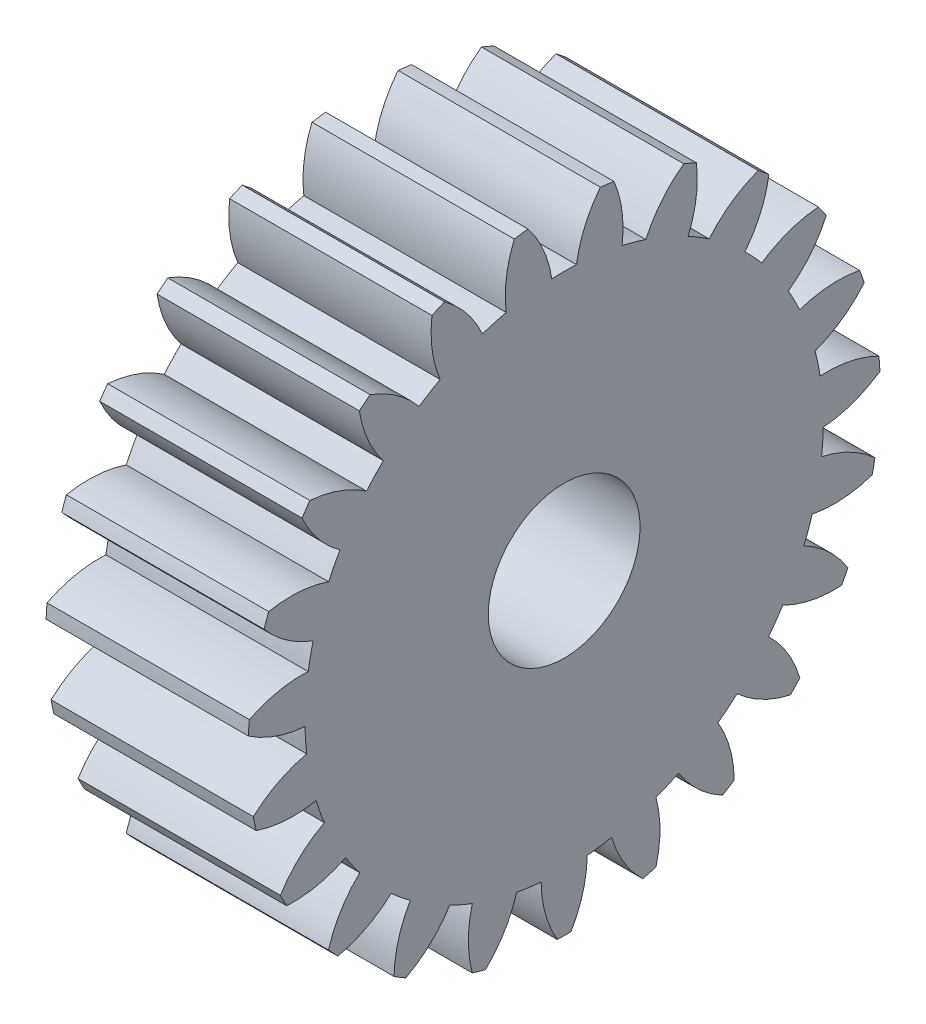
SolidWorks part; units mm, degrees
ref_plane "Plane1" through (0, 0, 0) normal (0, 0, 1) x (1, 0, 0)
ref_plane "Plane2" through (0, 0, 0) normal (0, 1, 0) x (1, 0, 0)
ref_plane "Plane3" through (0, 0, 0) normal (1, 0, 0) x (0, 0, -1)
other "Configuration Table"
sketch "HoldingSke" plane through (0, 0, 0) normal (0, 1, 0) x (1, 0, 0)
  line L0 (0, 0) -> (0.9205, -0.3907)
  line L1 (-15, 0) -> (100, 0) construction
  line L2 (0, 0) -> (-2.1039, 2.3779)
  line L3 (0, 0) -> (-11.863, 4.5341)
  line L4 (0, 0) -> (7.9495, 3.3744)
  line L5 (0, 0) -> (-46.8476, -17.4728)
  line L6 (0, 0) -> (-6.6317, -4.4744)
  line L7 (-2.1039, 2.3779) -> (8.6586, 51.2059)
  line L8 (-76.2, 54.61) -> (-75.2, 54.61)
  line L9 (-71.009, 38.7566) -> (-53.1078, 45.2721)
  line L10 (-76.2, 71.12) -> (104.1128, 71.12)
  line L11 (0, 0) -> (-8, 0)
  line L12 (-76.2, 101.6) -> (-76.162, 101.6)
  line L13 (24.9733, 27.94) -> (52.9518, 28.4284)
  line L14 (24.9733, 27.94) -> (24.9743, 27.94)
  line L15 (24.9733, 27.94) -> (100.4006, 29.5858)
  line L16 (-63.627, -1) -> (-12.827, -1)
  circle A0 centre (0, 0) radius 3
  circle A1 centre (0, 0) radius 10.249
  circle A2 centre (0, 0) radius 37.5
  circle A3 centre (0, 0) radius 3
  dimension "MHD" = 20.498
  dimension "Hub_dia" = 75
  dimension "Bore" = 6
  dimension "MBD" = 6
  dimension "Num_teeth" = 23
  dimension "Pitch" = 1
  dimension "Overall_len" = 50
  dimension "Show_teeth" = 23
  dimension "Thickness" = 8
  dimension "OAL" = 50.0001
  dimension "T_dim" = 1
  dimension "Ap" = 20
  dimension "H" = 19.05
  dimension "Pitch_radius" = 180.3128
  dimension "Width" = 8
  dimension "Backlash" = 0.038
  dimension "Addendum_fac" = 1
  dimension "Dedendum_fac" = 1.25
  dimension "Clearance_fac" = 0.25
  dimension "Dedendum_add" = 0.001
  dimension "Module" = 1
sketch "BasProSke" plane through (0, 0, 0) normal (0, 1, 0) x (1, 0, 0)
  line L0 (-10, 0) -> (60, 0) construction
  line L1 (0, 0) -> (0, 12.5)
  line L2 (0, 0) -> (8, 0)
  line L3 (8, 0) -> (8, 12.5)
  line L4 (8, 12.5) -> (0, 12.5)
  dimension "Thickness" = 8
  dimension "Diameter" = 25
revolve "Base-Revolve" add sketch "BasProSke" angle 360 about L0
sketch "TooCutSke" plane through (0, 0, 0) normal (1, 0, 0) x (0, 0, -1)
  line L1 (0, 0) -> (0, 107) construction
  line L2 (0, 0) -> (-0.8513, 11.4685) construction
  line L3 (0, 0) -> (-3.1257, 22.7413) construction
  line L4 (-0.8513, 11.4685) -> (-1.5629, 11.3706) construction
  arc A0 (0.4871, 10.2374) -> (-0.4871, 10.2374) centre (0, 0) ccw
  arc A1 (1.4505, 12.4411) -> (-1.4505, 12.4411) centre (0, 0) ccw
  circle A2 centre (0, 0) radius 11.5 construction
  circle A3 centre (0, 0) radius 10.8065 construction
  arc A4 (-0.4871, 10.2374) -> (-1.4505, 12.4411) centre (-5.037, 9.5608) ccw
  arc A5 (1.4505, 12.4411) -> (0.4871, 10.2374) centre (5.037, 9.5608) ccw
  dimension "Root_dia" = 20.498
  dimension "Overcut_dia" = 25.0508
  dimension "Pitch_dia" = 23
  dimension "Base_dia" = 21.6129
  dimension "Flank_rad" = 4.6
  dimension "Half_ang" = 7.826
  dimension "Half_CT" = 0.7183
extrude "ToothCut" cut sketch "TooCutSke" along normal through all
fillet "Breaks" [suppressed] radius 0.02
fillet "RootFillets" [suppressed] radius 0.251
pattern_circular "TeethCuts" count 23 every 15.652 about axis through (-10, 0, 0) along (1, 0, 0) of "ToothCut", "RootFillets", "Breaks"
sketch "HubNeaOneSke" plane through (0, 0, 0) normal (-1, 0, 0) x (0, 0, 1)
  circle A0 centre (0, 0) radius 10.249
  dimension "Diameter" = 20.498
extrude "HubNearOne" [suppressed] add sketch "HubNeaOneSke" along normal blind 42.0001
sketch "HubNeaBotSke" plane through (0, 0, 0) normal (-1, 0, 0) x (0, 0, 1)
  circle A0 centre (0, 0) radius 10.249
  dimension "Diameter" = 20.498
extrude "HubNearBoth" [suppressed] add sketch "HubNeaBotSke" along normal blind 21
ref_plane "FarPln" through (8, 0, 0) normal (1, 0, 0) x (0, 0, -1)
sketch "HubFarSke" plane through (8, 0, 0) normal (1, 0, 0) x (0, 0, -1)
  circle A0 centre (0, 0) radius 10.249
  dimension "Diameter" = 20.498
extrude "HubFar" [suppressed] add sketch "HubFarSke" along normal blind 21
sketch "BorSke" plane through (0, 0, 0) normal (1, 0, 0) x (0, 0, -1)
  circle A0 centre (0, 0) radius 3
  dimension "Diameter" = 6
extrude "Bore" cut sketch "BorSke" along normal mid plane 100.0001
sketch "KeySke" plane through (0, 0, 0) normal (1, 0, 0) x (0, 0, -1)
  line L0 (-1, 0) -> (-1, 4)
  line L1 (-1, 4) -> (1, 4)
  line L2 (1, 4) -> (1, 0)
  line L3 (0, 0) -> (0, 34) construction
  line L4 (-1, 0) -> (1, 0)
  dimension "Offset" = 4
  dimension "Width" = 2
extrude "Keyway" [suppressed] cut sketch "KeySke" along normal mid plane 100.0001
pattern_circular "Keyway2" [suppressed] count 2 every 90 about axis through (-10, 0, 0) along (1, 0, 0)
equation "' \"Module@HoldingSke\" = 6.35"
equation "' \"Num_teeth@HoldingSke\" = 12"
equation "' \"Ap@HoldingSke\" =  20"
equation "' \"Ap@HoldingSke\" = 20"
equation "' \"Width@HoldingSke\" = 0.5 * 25.4"
equation "' \"Hub_dia@HoldingSke\"= 1 * 25.4"
equation "' \"Hub_dia@HoldingSke\" = 1 * 25.4"
equation "' \"Overall_len@HoldingSke\" = 1.0 * 25.4"
equation "' \"Bore@HoldingSke\" = 0.75 * 25.4"
equation "' \"T_dim@HoldingSke\" = 0.1 * 25.4"
equation "' \"Width@KeySke\" = 0.25 * 25.4"
equation "' \"Show_teeth@HoldingSke\" = 13"
equation "' \"Backlash@HoldingSke\" = 0.009 * 25.4"
equation "' \"Addendum_fac@HoldingSke\" = 1.0"
equation "' \"Dedendum_fac@HoldingSke\" = 1.25"
equation "' \"Dedendum_add@HoldingSke\" = 0.00005 * 25.4"
equation "' \"Clearance_fac@HoldingSke\" = 0.25"
equation "\"Pitch@HoldingSke\" = 1 / \"Module@HoldingSke\""
equation "\"Overcut_dia@TooCutSke\" = (\"Num_teeth@HoldingSke\" + 2 * \"Addendum_fac@HoldingSke\") / \"Pitch@HoldingSke\" + 0.002 * 25.4"
equation "\"Pitch_dia@TooCutSke\" = \"Num_teeth@HoldingSke\" / \"Pitch@HoldingSke\""
equation "\"Base_dia@TooCutSke\" = \"Num_teeth@HoldingSke\" / \"Pitch@HoldingSke\" * cos((\"Ap@HoldingSke\"  * 3.14159265 / 180))"
equation "\"Root_dia@TooCutSke\" = (\"Num_teeth@HoldingSke\" + 2) / \"Pitch@HoldingSke\" - 2 * (\"Addendum_fac@HoldingSke\" + \"Dedendum_fac@HoldingSke\") / \"Pitch@HoldingSke\" - \"Dedendum_add@HoldingSke\" * 2"
equation "\"Half_ang@TooCutSke\" = 180 / \"Num_teeth@HoldingSke\""
equation "\"Half_CT@TooCutSke\" = \"Num_teeth@HoldingSke\" / \"Pitch@HoldingSke\" * sin((3.14159265 / 2 / \"Num_teeth@HoldingSke\")) / 2 - 7 * \"Backlash@HoldingSke\" / 4"
equation "\"Flank_rad@TooCutSke\" = \"Num_teeth@HoldingSke\" / \"Pitch@HoldingSke\" / 5"
equation "\"Radius@RootFillets\" = \"Clearance_fac@HoldingSke\" / \"Pitch@HoldingSke\" + \"Dedendum_add@HoldingSke\""
equation "\"Break_rad@Breaks\" = 0.02 / \"Pitch@HoldingSke\""
equation "\"Thickness@HoldingSke\" = \"Width@HoldingSke\""
equation "\"OAL@HoldingSke\" = \"Thickness@HoldingSke\""
equation "\"MHD@HoldingSke\" = (\"Num_teeth@HoldingSke\" + 2) / \"Pitch@HoldingSke\" - 2 * (\"Addendum_fac@HoldingSke\" + \"Dedendum_fac@HoldingSke\")  / \"Pitch@HoldingSke\" - \"Dedendum_add@HoldingSke\" * 2"
equation "\"MBD@HoldingSke\" = (\"Num_teeth@HoldingSke\" + 2) / \"Pitch@HoldingSke\" - 2 * (\"Addendum_fac@HoldingSke\" + \"Dedendum_fac@HoldingSke\")  / \"Pitch@HoldingSke\" - \"Dedendum_add@HoldingSke\" * 2 - 0.002 * 25.4"
equation "\"MHD@HoldingSke\" = ((sgn( \"MHD@HoldingSke\" - \"Hub_dia@HoldingSke\" )-1)*( \"MHD@HoldingSke\" - \"Hub_dia@HoldingSke\" ))/-2+ \"Hub_dia@HoldingSke\""
equation "\"MBD@HoldingSke\" = ((sgn( \"MBD@HoldingSke\" - \"Bore@HoldingSke\" )-1)*( \"MBD@HoldingSke\" - \"Bore@HoldingSke\" ))/-2+ \"Bore@HoldingSke\""
equation "\"OAL@HoldingSke\" = ((sgn( \"OAL@HoldingSke\" - \"Overall_len@HoldingSke\" )+1)*( \"OAL@HoldingSke\" - \"Overall_len@HoldingSke\" ))/2 + \"Overall_len@HoldingSke\" + 0.000002 * 25.4"
equation "\"Num_teeth@TeethCuts\" = int( \"Show_teeth@HoldingSke\" ) + 1"
equation "\"Num_teeth@TeethCuts\" = ((sgn( \"Num_teeth@TeethCuts\" - \"Num_teeth@HoldingSke\" )-1)*( \"Num_teeth@TeethCuts\" - \"Num_teeth@HoldingSke\" ))/-2+ \"Num_teeth@HoldingSke\""
equation "\"Num_teeth@TeethCuts\" = ((sgn( \"Num_teeth@TeethCuts\" - 2.0)+1)*( \"Num_teeth@TeethCuts\" - 2.0))/2 +2.0"
equation "\"Angle@TeethCuts\" = 360.0 / \"Num_teeth@HoldingSke\""
equation "\"Diameter@BasProSke\" = (\"Num_teeth@HoldingSke\" + 2 * \"Addendum_fac@HoldingSke\") / \"Pitch@HoldingSke\""
equation "\"Thickness@BasProSke\"  = \"Thickness@HoldingSke\""
equation "' \"Fillet_rad@BasProSke\" =  \"Thickness@HoldingSke\" * 0.05"
equation "' \"Fillet_rad@BasProSke\" = \"Thickness@HoldingSke\" * 0.05"
equation "\"MHD@HoldingSke\" = ((sgn( \"MHD@HoldingSke\" - \"Root_dia@TooCutSke\" )-1)*( \"MHD@HoldingSke\" - \"Root_dia@TooCutSke\" ))/-2+ \"Root_dia@TooCutSke\""
equation "\"Diameter@HubNeaOneSke\" = \"MHD@HoldingSke\""
equation "\"Length@HubNearOne\" = \"OAL@HoldingSke\" - \"Thickness@BasProSke\""
equation "\"Diameter@HubNeaBotSke\" = \"MHD@HoldingSke\""
equation "\"Length@HubNearBoth\" = ( \"OAL@HoldingSke\" - \"Thickness@BasProSke\" ) / 2.0"
equation "\"Thickness@FarPln\" = \"Thickness@BasProSke\""
equation "\"Diameter@HubFarSke\" = \"MHD@HoldingSke\""
equation "\"Length@HubFar\" = ( \"OAL@HoldingSke\" - \"Thickness@BasProSke\" ) / 2.0"
equation "\"Diameter@BorSke\" = \"MBD@HoldingSke\""
equation "\"D1@Bore\" = \"OAL@HoldingSke\" * 2.0"
equation "\"D1@Keyway\" = \"OAL@HoldingSke\" * 2.0"
equation "\"Offset@KeySke\" = \"T_dim@HoldingSke\" + \"MBD@HoldingSke\" / 2.0"
